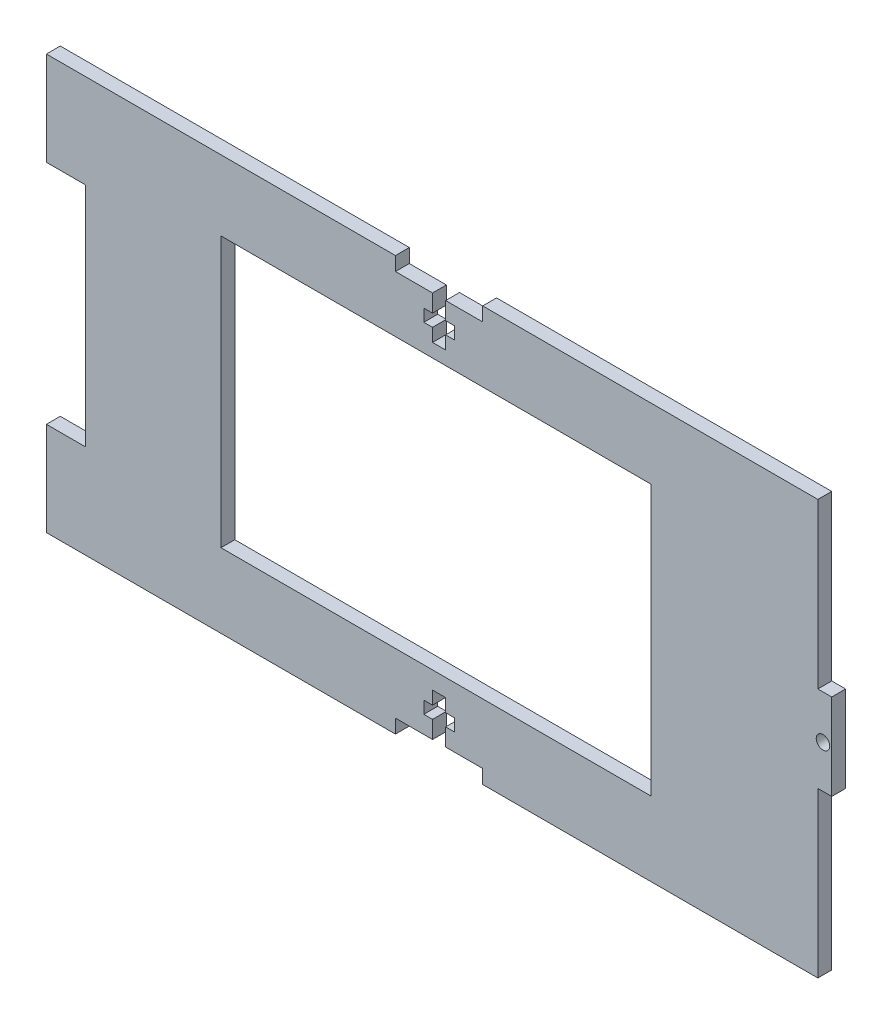
SolidWorks part; units mm, degrees
ref_plane "Front Plane" through (0, 0, 0) normal (0, 0, 1) x (1, 0, 0)
ref_plane "Top Plane" through (0, 0, 0) normal (0, 1, 0) x (1, 0, 0)
ref_plane "Right Plane" through (0, 0, 0) normal (1, 0, 0) x (0, 0, -1)
sketch "Sketch1" plane through (0, 0, 0) normal (0, 0, 1) x (1, 0, 0)
  line L1 (-90, 47.5) -> (90, 47.5)
  line L2 (-90, 47.5) -> (-90, -47.5)
  line L3 (-90, -47.5) -> (90, -47.5)
  line L4 (90, 47.5) -> (90, -47.5)
  dimension "D1" = 180
  dimension "D2" = 95
  dimension "D3" = 47.5
  dimension "D4" = 90
extrude "Boss-Extrude1" add sketch "Sketch1" along normal blind 3.18
sketch "Sketch2" plane through (0, 0, 3.18) normal (0, 0, 1) x (1, 0, 0)
  line L1 (90, 47.5) -> (86.82, 47.5)
  line L2 (90, 47.5) -> (90, 9.875)
  line L3 (90, 9.875) -> (86.82, 9.875)
  line L4 (86.82, 47.5) -> (86.82, 9.875)
  dimension "D1" = 3.18
  dimension "D2" = 37.625
extrude "Cut-Extrude1" cut sketch "Sketch2" against normal through all both and the other way through all
mirror "Mirror1" about plane through (0, 0, 0) normal (0, 1, 0) of "Cut-Extrude1"
sketch "Sketch3" plane through (0, 0, 3.18) normal (0, 0, 1) x (1, 0, 0)
  line L0 (90, -9.875) -> (90, 9.875) construction
  line L2 (86.82, 9.875) -> (90, 9.875) construction
  circle A0 centre (88, -0.125) radius 1.55
  dimension "D1" = 3.1
  dimension "D2" = 2
  dimension "D3" = 10
extrude "Cut-Extrude2" cut sketch "Sketch3" against normal through all both and the other way through all
sketch "Sketch4" plane through (0, 0, 3.18) normal (0, 0, 1) x (1, 0, 0)
  line L0 (-90, -47.5) -> (86.82, -47.5) construction
  line L1 (-10, -47.5) -> (10, -47.5)
  line L2 (-10, -47.5) -> (-10, -44.32)
  line L3 (-10, -44.32) -> (-1.5, -44.32)
  line L4 (10, -47.5) -> (10, -44.32)
  line L5 (-90, 47.5) -> (-90, -47.5) construction
  line L6 (1.5, -37.5) -> (3.5, -37.5)
  line L8 (-1.5, -44.32) -> (-1.5, -40.3188)
  line L9 (-1.5, -34.5) -> (1.5, -34.5)
  line L10 (1.5, -44.32) -> (1.5, -40.3188)
  line L11 (-3.5, -37.5) -> (-1.5, -37.5)
  line L12 (-3.5, -37.5) -> (-3.5, -40.3188)
  line L13 (-3.5, -40.3188) -> (-1.5, -40.3188)
  line L14 (3.5, -37.5) -> (3.5, -40.3188)
  line L15 (-1.5, -37.5) -> (-1.5, -34.5)
  line L16 (1.5, -37.5) -> (1.5, -34.5)
  line L17 (1.5, -40.3188) -> (3.5, -40.3188)
  line L18 (1.5, -44.32) -> (10, -44.32)
  dimension "D1" = 20
  dimension "D2" = 80
  dimension "D3" = 3.18
  dimension "D4" = 3
  dimension "D5" = 9.82
  dimension "D6" = 7
  dimension "D7" = 2.8188
  dimension "D8" = 2
  dimension "D9" = 3
  dimension "D10" = 8.5
extrude "Cut-Extrude3" cut sketch "Sketch4" against normal through all both and the other way through all
mirror "Mirror2" about plane through (0, 0, 0) normal (0, 1, 0) of "Cut-Extrude3"
sketch "Sketch7" plane through (0, 0, 0) normal (0, 0, -1) x (-1, 0, 0)
  line L0 (-1.5, -34.5) -> (1.5, -34.5) construction
  line L1 (-48.6, 31.4) -> (50, 31.4)
  line L2 (-48.6, 31.4) -> (-48.6, -30.5)
  line L3 (-48.6, -30.5) -> (50, -30.5)
  line L4 (50, 31.4) -> (50, -30.5)
  line L5 (90, 47.5) -> (90, -47.5) construction
  dimension "D1" = 98.6
  dimension "D2" = 61.9
  dimension "D3" = 4
  dimension "D4" = 40
extrude "Cut-Extrude6" cut sketch "Sketch7" against normal through all both and the other way through all
sketch "Sketch8" plane through (0, 0, 0) normal (0, 0, -1) x (-1, 0, 0)
  line L0 (90, 47.5) -> (90, -47.5) construction
  line L1 (90, 26) -> (81, 26)
  line L2 (90, 26) -> (90, -26)
  line L3 (90, -26) -> (81, -26)
  line L4 (81, 26) -> (81, -26)
  line L5 (90, -47.5) -> (10, -47.5) construction
  dimension "D1" = 52
  dimension "D2" = 9
  dimension "D3" = 21.5
extrude "Cut-Extrude7" cut sketch "Sketch8" against normal through all both and the other way through all
